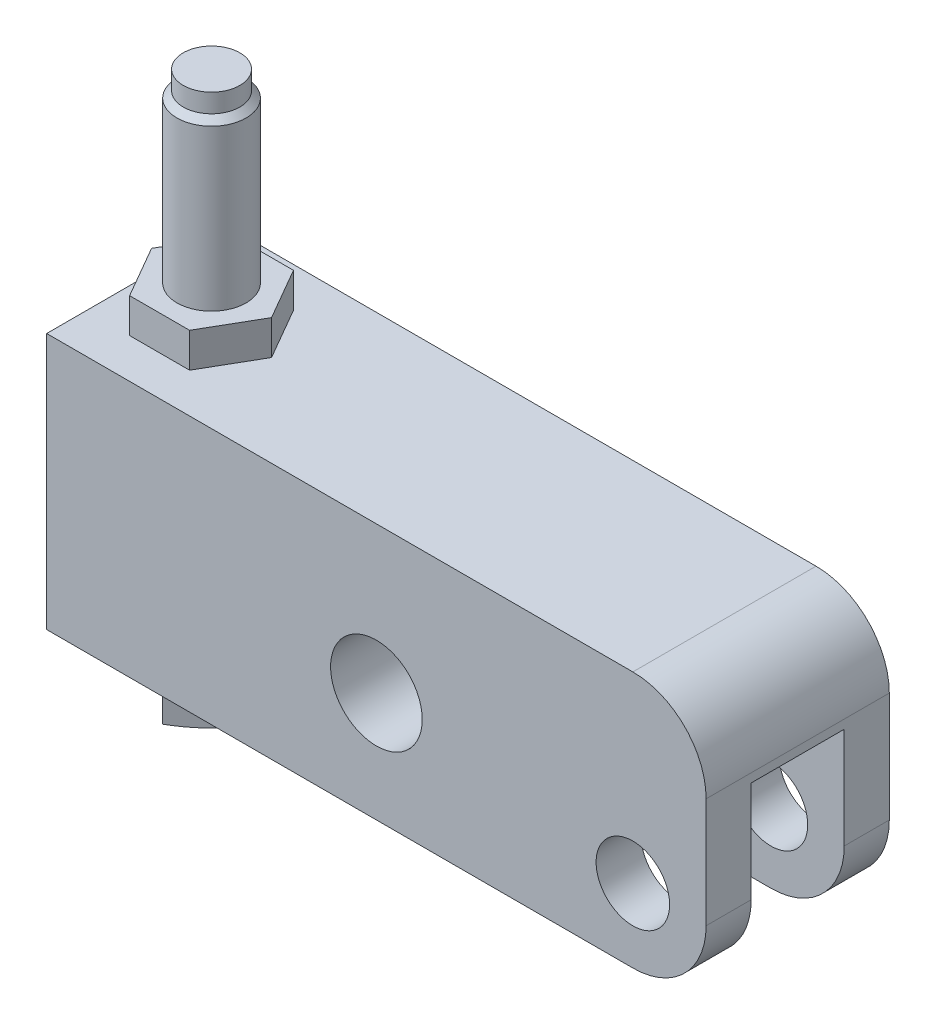
SolidWorks part; units mm, degrees
material "Alloy Steel"
ref_plane "Front Plane" through (0, 0, 0) normal (0, 0, 1) x (1, 0, 0)
ref_plane "Top Plane" through (0, 0, 0) normal (0, 1, 0) x (1, 0, 0)
ref_plane "Right Plane" through (0, 0, 0) normal (1, 0, 0) x (0, 0, -1)
sketch "Sketch11" plane through (0, 0, 0) normal (0, 0, 1) x (1, 0, 0)
  line L1 (-101.6, 31.75) -> (12.7, 31.75)
  line L2 (-101.6, 31.75) -> (-101.6, -12.7)
  line L3 (-101.6, -12.7) -> (12.7, -12.7)
  line L4 (12.7, 31.75) -> (12.7, -12.7)
  circle A0 centre (0, 0) radius 6.369
  circle A1 centre (-44.45, 6.35) radius 7.9438
  dimension "D1" = 12.7381
  dimension "D6" = 15.8877
  dimension "D2" = 12.7
  dimension "D3" = 101.6
  dimension "D4" = 44.45
  dimension "D5" = 44.45
  dimension "D7" = 12.7
  dimension "D8" = 6.35
extrude "Extrude3" add sketch "Sketch11" along normal mid plane 31.75
sketch "Sketch12" plane through (0, -12.7, 0) normal (0, -1, 0) x (1, 0, 0)
  line L0 (0, 0) -> (-16.2248, 0) construction
  line L1 (-17.526, 8.0645) -> (12.7, 8.0645)
  line L2 (12.7, 15.875) -> (12.7, -15.875) construction
  line L3 (12.7, 8.0645) -> (12.7, -8.0645)
  line L4 (-101.6, 15.875) -> (12.7, 15.875) construction
  line L5 (-17.526, -8.0645) -> (12.7, -8.0645)
  arc A0 (-17.526, 8.0645) -> (-17.526, -8.0645) centre (-17.526, 0) ccw
  dimension "D3" = 38.2905
  dimension "D1" = 16.129
  dimension "D2" = 7.8105
extrude "Cut-Extrude1" cut sketch "Sketch12" against normal blind 30.226
fillet "Fillet1" radius 12.7 3 edges at (12.7, 31.75, 0) (12.7, -12.7, -11.9697) (12.7, -12.7, 11.9697)
sketch "Sketch13" plane through (0, 31.75, 0) normal (0, 1, 0) x (1, 0, 0)
  line L1 (-78.5027, 0) -> (-83.7014, 9.0043)
  line L2 (-83.7014, 9.0043) -> (-94.0986, 9.0043)
  line L3 (-94.0986, 9.0043) -> (-99.2973, 0)
  line L4 (-99.2973, 0) -> (-94.0986, -9.0043)
  line L5 (-94.0986, -9.0043) -> (-83.7014, -9.0043)
  line L6 (-83.7014, -9.0043) -> (-78.5027, 0)
  circle A0 centre (-88.9, 0) radius 9.0043 construction
  dimension "D1" = 18.0086
  dimension "D2" = 88.9
extrude "Extrude4" add sketch "Sketch13" along normal blind 5.9944
sketch "Sketch14" plane through (0, 0, 0) normal (0, 0, 1) x (1, 0, 0)
  line L0 (-88.9, 71.229) -> (-88.9, -12.9942) construction
  line L1 (-78.5027, 37.7444) -> (-78.5027, 31.75) construction
  line L2 (-99.2973, 37.7444) -> (-99.2973, 31.75) construction
  line L3 (-93.8022, 66.5988) -> (-93.8022, 69.85)
  line L4 (-93.8022, 66.5988) -> (-94.8944, 65.5066)
  line L5 (-94.8944, 65.5066) -> (-94.8944, -13.4112)
  line L6 (-94.8944, -13.4112) -> (-113.1252, -13.4112)
  line L7 (-113.1252, -13.4112) -> (-113.1252, -14.1732)
  line L8 (-93.8022, 69.85) -> (-88.9, 69.85)
  line L9 (-88.9, 69.85) -> (-88.9, -25.4)
  line L10 (-101.6, -12.7) -> (0, -12.7) construction
  arc A0 (-113.1252, -14.1732) -> (-88.9, -25.4) centre (-88.9, 6.35) ccw
  dimension "D5" = 31.75
  dimension "D2" = 9.8044
  dimension "D3" = 45
  dimension "D4" = 80.01
  dimension "D6" = 12.7
  dimension "D7" = 11.9888
  dimension "D8" = 0.762
  dimension "D9" = 11.9888
  dimension "D10" = 88.9
  dimension "D11" = 3.2512
revolve "Revolve2" add sketch "Sketch14" angle 360 about L0
sketch "Sketch15" plane through (0, -13.4112, 0) normal (0, 1, 0) x (1, 0, 0)
  line L0 (-80.4226, 0) -> (-97.3774, 0) construction
  line L1 (-88.9, 8.4774) -> (-97.3774, 0)
  line L2 (-97.3774, 0) -> (-88.9, -8.4774)
  line L3 (-88.9, -8.4774) -> (-80.4226, 0)
  line L4 (-80.4226, 0) -> (-88.9, 8.4774)
  circle A0 centre (-88.9, 0) radius 5.9944 construction
  circle A1 centre (-88.9, 0) radius 24.2252 construction
  circle A2 centre (-88.9, 0) radius 24.2252
  dimension "D1" = 11.9888
extrude "Cut-Extrude2" cut sketch "Sketch15" against normal through all
